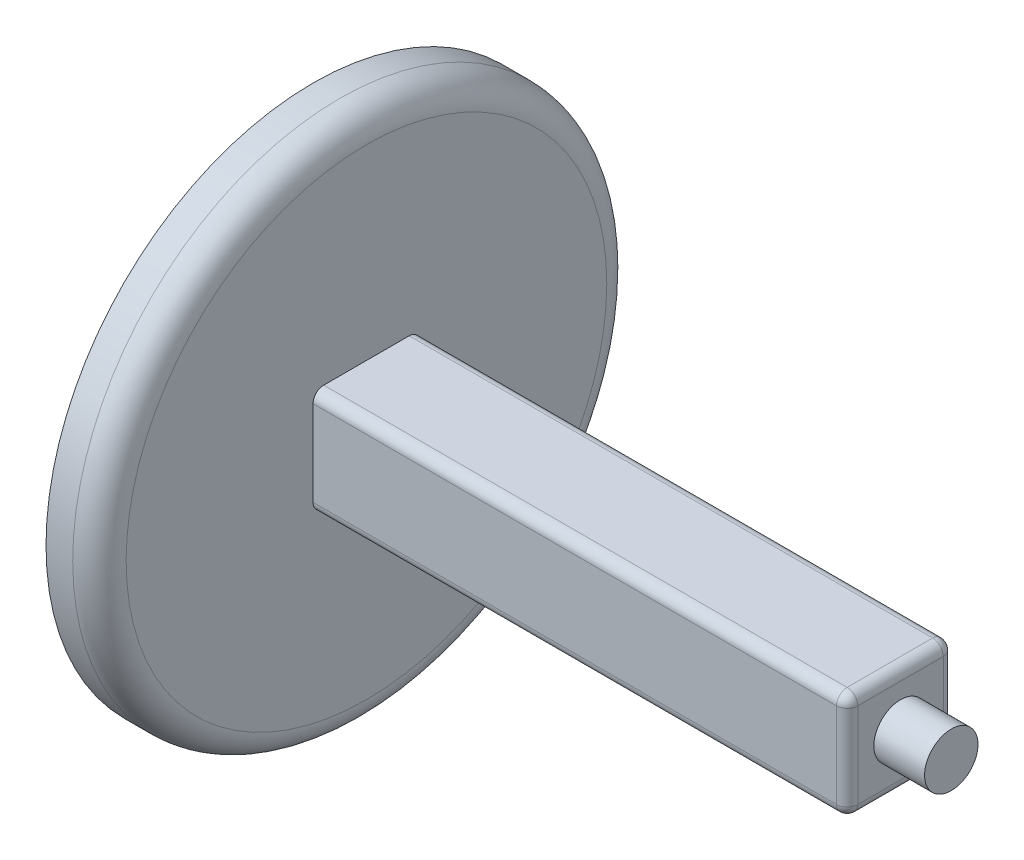
SolidWorks part; units mm, degrees
ref_plane "Plan de face" through (0, 0, 0) normal (0, 0, 1) x (1, 0, 0)
ref_plane "Plan de dessus" through (0, 0, 0) normal (0, 1, 0) x (1, 0, 0)
ref_plane "Plan de droite" through (0, 0, 0) normal (1, 0, 0) x (0, 0, -1)
sketch "Esquisse1" plane through (0, 0, 0) normal (1, 0, 0) x (0, 0, -1)
  circle A0 centre (0, 0) radius 500
  dimension "D1" = 1000
extrude "Boss.-Extru.1" add sketch "Esquisse1" along normal blind 100
sketch "Esquisse2" plane through (100, 0, 0) normal (1, 0, 0) x (0, 0, -1)
  line L1 (-100, -100) -> (100, -100)
  line L2 (-100, -100) -> (-100, 100)
  line L3 (-100, 100) -> (100, 100)
  line L4 (100, -100) -> (100, 100)
  line L5 (-100, -100) -> (100, 100) construction
  line L6 (-100, 100) -> (100, -100) construction
  point P0 (0, 0)
  dimension "D1" = 200
  dimension "D2" = 200
extrude "Boss.-Extru.2" add sketch "Esquisse2" along normal blind 1000
sketch "Esquisse3" plane through (1100, 0, 0) normal (1, 0, 0) x (0, 0, -1)
  circle A0 centre (0, 0) radius 50
extrude "Boss.-Extru.3" add sketch "Esquisse3" along normal blind 95
fillet "Congé1" radius 50 1 edges at (100, 0, -500)
fillet "Congé2" radius 20 4 edges at (600, 100, -100) (600, -100, -100) (600, -100, 100) (600, 100, 100)
fillet "Congé3" radius 20 8 edges at (1100, 100, 0) (1100, 0, -100) (1100, -100, 0) (1100, 0, 100) (1100, -94.1421, -94.1421) (1100, -94.1421, 94.1421) (1100, 94.1421, -94.1421) (1100, 94.1421, 94.1421)
equation "\"D2@Esquisse2\"=\"D1@Esquisse2\""
